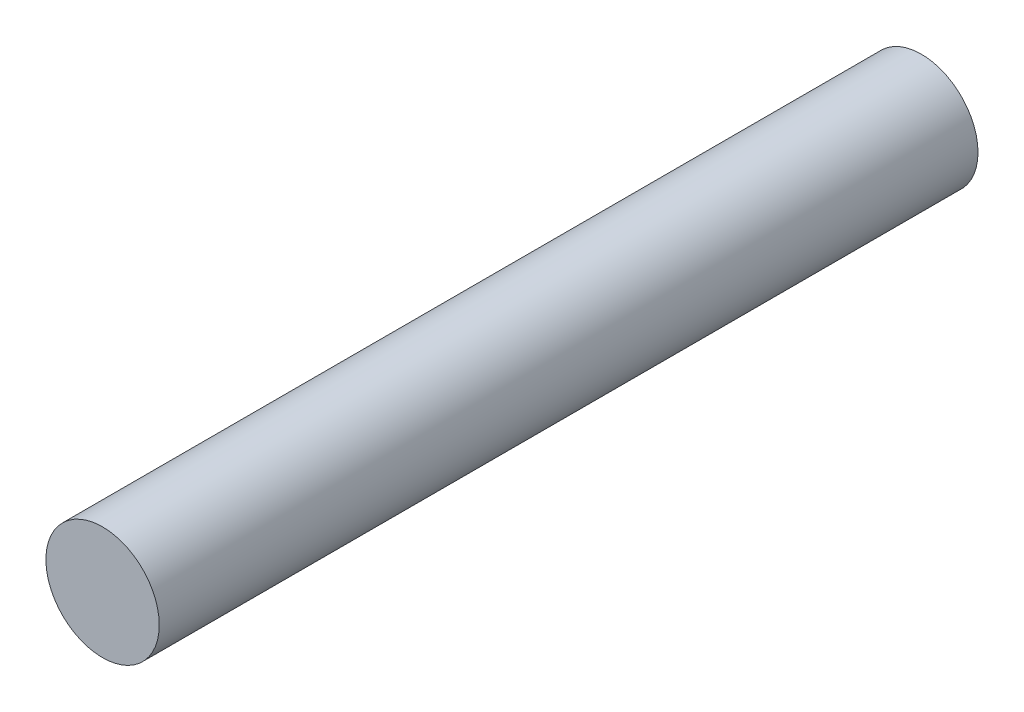
SolidWorks part; units mm, degrees
material "AISI 1020"
ref_plane "Front Plane" through (0, 0, 0) normal (0, 0, 1) x (1, 0, 0)
ref_plane "Top Plane" through (0, 0, 0) normal (0, 1, 0) x (1, 0, 0)
ref_plane "Right Plane" through (0, 0, 0) normal (1, 0, 0) x (0, 0, -1)
sketch "Sketch1" plane through (0, 0, 0) normal (0, 0, 1) x (1, 0, 0)
  circle A0 centre (0, 0) radius 4.572
  dimension "D1" = 9.144
extrude "Boss-Extrude1" add sketch "Sketch1" along normal blind 66.04
